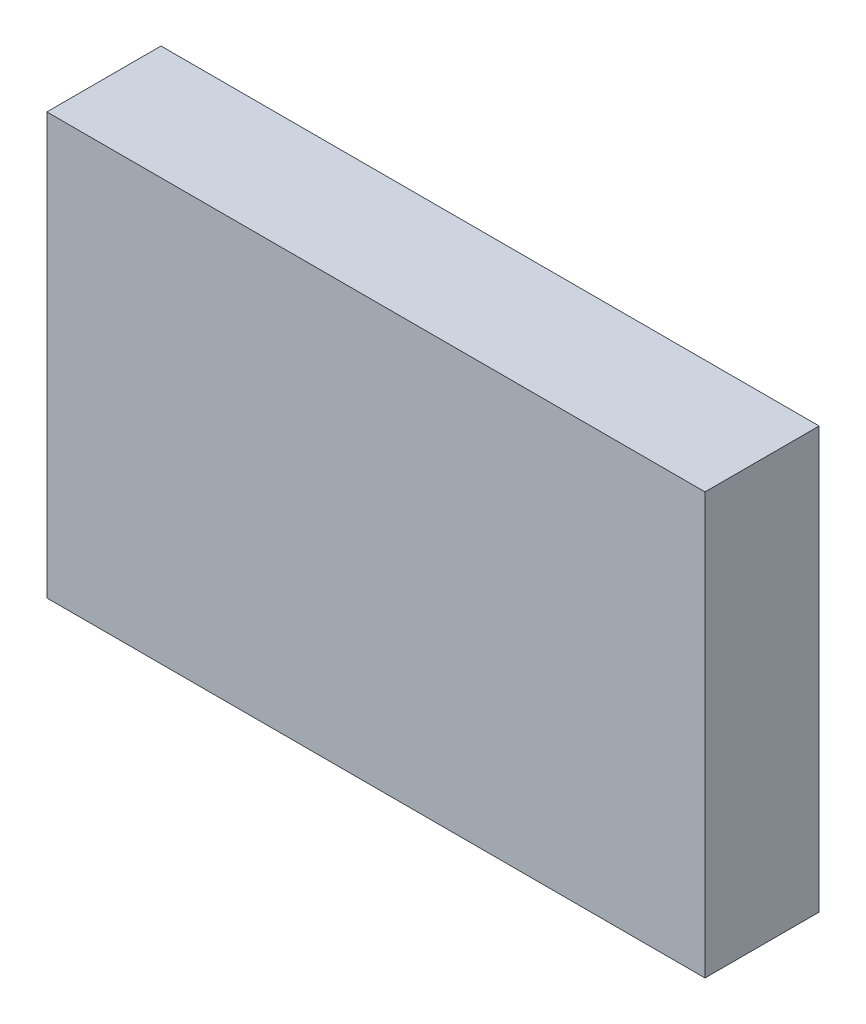
SolidWorks part; units mm, degrees
ref_plane "Plan de face" through (0, 0, 0) normal (0, 0, 1) x (1, 0, 0)
ref_plane "Plan de dessus" through (0, 0, 0) normal (0, 1, 0) x (1, 0, 0)
ref_plane "Plan de droite" through (0, 0, 0) normal (1, 0, 0) x (0, 0, -1)
sketch "Esquisse1" plane through (0, 0, 0) normal (0, 0, 1) x (1, 0, 0)
  line L1 (0, 0) -> (57.664, 0)
  line L2 (0, 0) -> (0, 36.8845)
  line L3 (0, 36.8845) -> (57.664, 36.8845)
  line L4 (57.664, 0) -> (57.664, 36.8845)
extrude "Boss.-Extru.1" add sketch "Esquisse1" along normal blind 10
ref_plane "Plan1" through (0, 0, 20) normal (0, 0, 1) x (1, 0, 0)
